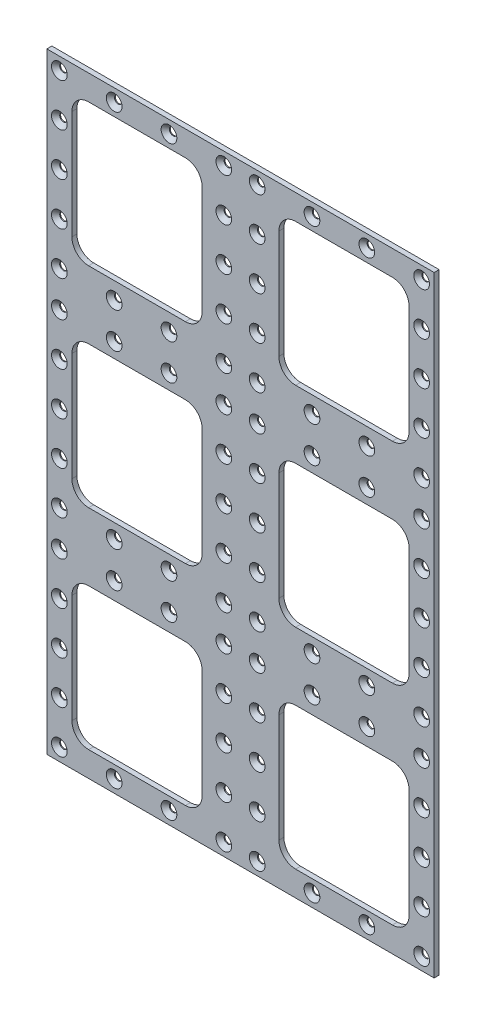
SolidWorks part; units mm, degrees
material "6061-T6 (SS)"
ref_plane "Alzado" through (0, 0, 0) normal (0, 0, 1) x (1, 0, 0)
ref_plane "Planta" through (0, 0, 0) normal (0, 1, 0) x (1, 0, 0)
ref_plane "Vista lateral" through (0, 0, 0) normal (1, 0, 0) x (0, 0, -1)
sketch "Sketch1" plane through (0, 0, 0) normal (0, 0, 1) x (1, 0, 0)
  line L1 (-116, 183) -> (116, 183)
  line L2 (-116, 183) -> (-116, -183)
  line L3 (-116, -183) -> (116, -183)
  line L4 (116, 183) -> (116, -183)
  line L5 (-116, 183) -> (116, -183) construction
  line L6 (-116, -183) -> (116, 183) construction
  point P0 (0, 0)
  dimension "D1" = 366
  dimension "D2" = 232
extrude "Boss-Extrude1" add sketch "Sketch1" along normal blind 3
sketch "Sketch2" plane through (0, 0, 0) normal (0, 0, 1) x (1, 0, 0)
  line L0 (0, 186.1376) -> (0, -191.1438) construction
  line L1 (-164.2926, 0) -> (162.9273, 0) construction
  line L2 (116, 183) -> (-116, 183) construction
  line L3 (-101, 168) -> (-23, 168)
  line L4 (-101, 168) -> (-101, 83)
  line L5 (-101, 83) -> (-23, 83)
  line L6 (-23, 168) -> (-23, 83)
  line L7 (-101, 168) -> (-23, 83) construction
  line L8 (-101, 83) -> (-23, 168) construction
  line L9 (-116, 183) -> (-116, -183) construction
  point P5 (-62, 125.5)
  dimension "D1" = 15
  dimension "D2" = 15
  dimension "D3" = 78
  dimension "D4" = 85
extrude "Cut-Extrude4" cut sketch "Sketch2" along normal through all
fillet "Fillet1" radius 10 4 edges at (-23, 83, 1.5) (-23, 168, 1.5) (-101, 83, 1.5) (-101, 168, 1.5)
pattern_linear "LPattern1" count 3 spacing 125.5 along (0, -1, 0) count 2 spacing 124 along (1, 0, 0) of "Cut-Extrude4", "Fillet1"
sketch "Sketch7" plane through (0, 0, 3) normal (0, 0, 1) x (1, 0, 0)
  line L0 (-116, 183) -> (-116, -183) construction
  line L1 (116, 183) -> (-116, 183) construction
  point P0 (-108.5, 175.5)
  dimension "D1" = 7.5
  dimension "D2" = 7.5
hole_wizard "CSK for M4 Flat Head Machine Screw3" positions "Sketch7" profile "Sketch8" countersink size "M4" standard "ANSI Metric" end condition through all
sketch "Sketch8" plane through (-108.5, 175.5, 3) normal (1, 0, 0) x (0, -1, 0)
  line L0 (0, 0) -> (0, 3)
  line L1 (0, 3) -> (2.25, 3)
  line L2 (2.25, 3) -> (2.25, 2.45)
  line L3 (2.25, 2.45) -> (4.7, 0)
  line L5 (4.7, 0) -> (0, 0)
  line L6 (-2.25, 2.45) -> (-4.7, 0) construction
  line L11 (0, -6.35) -> (0, 107.95) construction
  dimension "Thru Hole Dia." = 4.5
  dimension "Thru Hole Depth" = 3
  dimension "Near C'Sink Dia." = 9.4
  dimension "Near C'Sink Angle" = 90
sketch "Sketch9" plane through (0, 0, 3) normal (0, 0, 1) x (1, 0, 0)
  line L0 (0, 183) -> (0, -183) construction
  line L1 (116, 183) -> (-116, 183) construction
  line L2 (-116, -183) -> (116, -183) construction
  line L3 (-116, 62.75) -> (116, 62.75) construction
  line L4 (-116, -62.75) -> (116, -62.75) construction
  line L5 (-91, 83) -> (-33, 83) construction
  line L6 (-116, 183) -> (-116, -183) construction
  line L7 (116, -183) -> (116, 183) construction
  line L8 (-33, 42.5) -> (-91, 42.5) construction
  line L9 (-91, -42.5) -> (-33, -42.5) construction
  line L10 (-33, -83) -> (-91, -83) construction
pattern_linear "LPattern5" count 4 spacing 32.8333 along (1, 0, 0) count 5 spacing 25.6875 along (0, -1, 0) skipping (1, 1), (1, 2), (1, 3), (2, 1), (2, 2), (2, 3) of "CSK for M4 Flat Head Machine Screw3"
pattern_linear "LPattern6" count 3 spacing 124.125 along (0, -1, 0) of "LPattern5", "CSK for M4 Flat Head Machine Screw3"
mirror "Mirror1" about plane through (0, 0, 0) normal (1, 0, 0) of "LPattern6", "CSK for M4 Flat Head Machine Screw3", "LPattern5"
